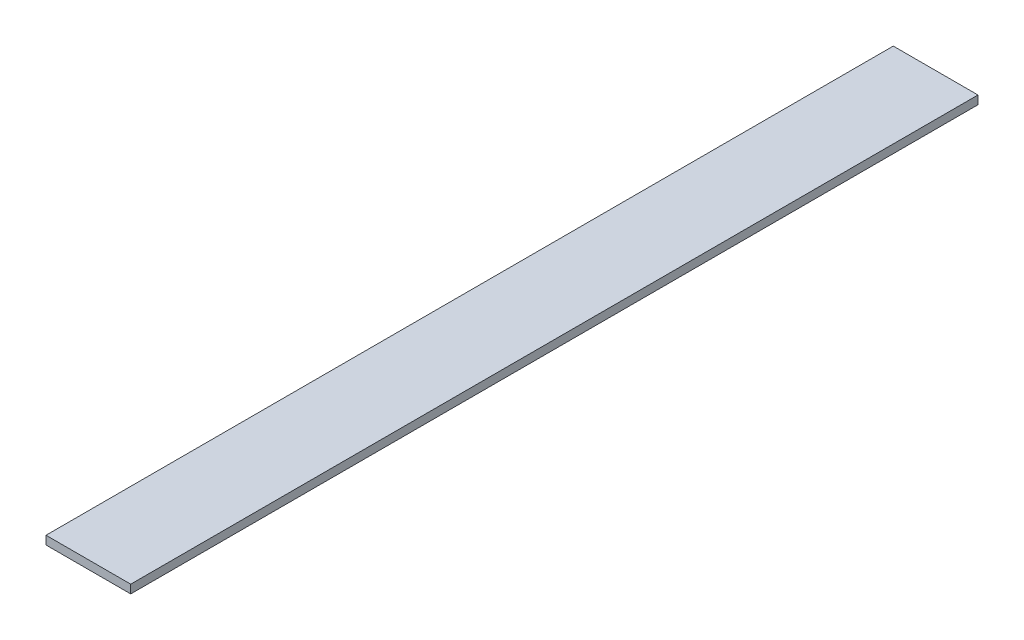
SolidWorks part; units mm, degrees
ref_plane "Front Plane" through (0, 0, 0) normal (0, 0, 1) x (1, 0, 0)
ref_plane "Top Plane" through (0, 0, 0) normal (0, 1, 0) x (1, 0, 0)
ref_plane "Right Plane" through (0, 0, 0) normal (1, 0, 0) x (0, 0, -1)
sketch "Sketch1" plane through (0, 0, 0) normal (0, 0, 1) x (1, 0, 0)
  line L1 (0, 0) -> (63.5, 0)
  line L2 (0, 0) -> (0, 6.35)
  line L3 (0, 6.35) -> (63.5, 6.35)
  line L4 (63.5, 0) -> (63.5, 6.35)
  dimension "D1" = 6.35
  dimension "D2" = 63.5
extrude "Boss-Extrude1" add sketch "Sketch1" along normal blind 635
